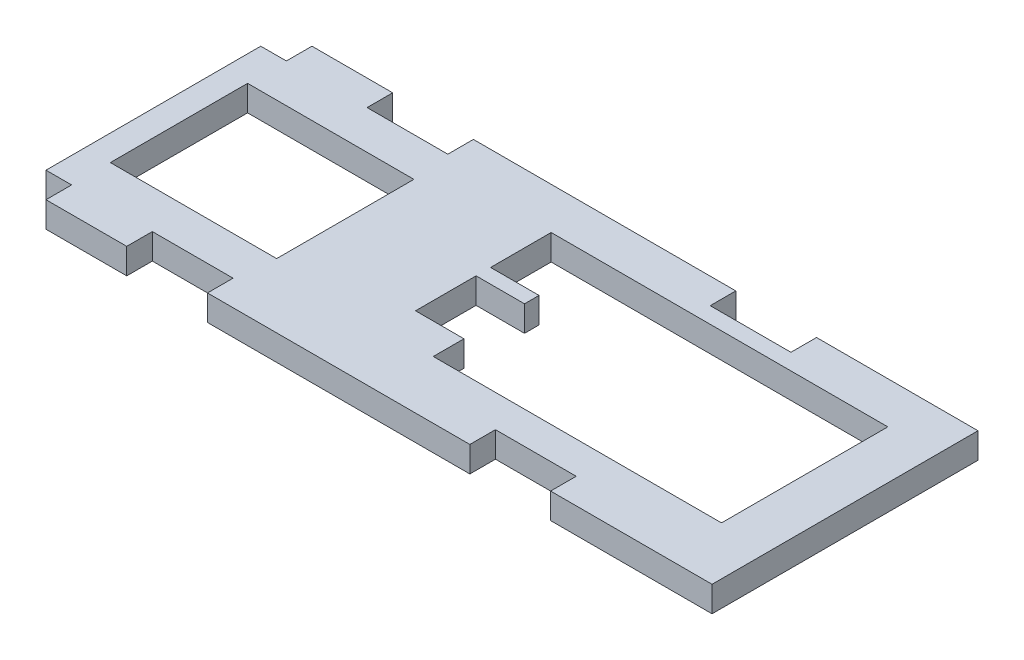
SolidWorks part; units mm, degrees
ref_plane "Front Plane" through (0, 0, 0) normal (0, 0, 1) x (1, 0, 0)
ref_plane "Top Plane" through (0, 0, 0) normal (0, 1, 0) x (1, 0, 0)
ref_plane "Right Plane" through (0, 0, 0) normal (1, 0, 0) x (0, 0, -1)
sketch "Sketch1" plane through (0, 0, 0) normal (0, 1, 0) x (1, 0, 0)
  line L0 (55.67, 32.94) -> (65.67, 32.94)
  line L1 (0, 0) -> (85.67, 0)
  line L2 (0, 0) -> (0, 32.94)
  line L3 (0, 32.94) -> (85.67, 32.94)
  line L4 (85.67, 0) -> (85.67, 32.94)
  line L5 (13.17, 3.17) -> (23.17, 3.17)
  line L6 (13.17, 3.17) -> (13.17, 0)
  line L7 (13.17, 0) -> (23.17, 0)
  line L8 (23.17, 3.17) -> (23.17, 0)
  line L9 (13.17, 32.94) -> (23.17, 32.94)
  line L10 (13.17, 32.94) -> (13.17, 29.77)
  line L11 (13.17, 29.77) -> (23.17, 29.77)
  line L12 (23.17, 32.94) -> (23.17, 29.77)
  line L13 (55.67, 32.94) -> (55.67, 29.77)
  line L14 (55.67, 29.77) -> (65.67, 29.77)
  line L15 (65.67, 32.94) -> (65.67, 29.77)
  line L16 (55.67, 3.17) -> (65.67, 3.17)
  line L17 (55.67, 3.17) -> (55.67, 0)
  line L18 (55.67, 0) -> (65.67, 0)
  line L19 (65.67, 3.17) -> (65.67, 0)
  line L25 (3.17, 24.97) -> (23.77, 24.97)
  line L26 (3.17, 24.97) -> (3.17, 7.97)
  line L27 (3.17, 7.97) -> (23.77, 7.97)
  line L28 (23.77, 24.97) -> (23.77, 7.97)
  line L29 (43.97, 27.77) -> (79.67, 27.77)
  line L30 (43.97, 27.77) -> (43.97, 7.17)
  line L31 (43.97, 7.17) -> (79.67, 7.17)
  line L32 (79.67, 27.77) -> (79.67, 7.17)
  line L33 (43.97, 10.97) -> (37.97, 10.97)
  line L34 (43.97, 10.97) -> (43.97, 18.47)
  line L35 (43.97, 18.47) -> (37.97, 18.47)
  line L36 (37.97, 10.97) -> (37.97, 18.47)
  line L37 (0, 32.94) -> (3.17, 32.94)
  line L38 (0, 32.94) -> (0, 29.77)
  line L39 (0, 29.77) -> (3.17, 29.77)
  line L40 (3.17, 32.94) -> (3.17, 29.77)
  line L41 (0, 0) -> (3.17, 0)
  line L42 (0, 0) -> (0, 3.17)
  line L43 (0, 3.17) -> (3.17, 3.17)
  line L44 (3.17, 0) -> (3.17, 3.17)
  line L45 (43.97, 20.27) -> (37.97, 20.27)
  line L46 (43.97, 20.27) -> (43.97, 27.77)
  line L47 (43.97, 27.77) -> (37.97, 27.77)
  line L48 (37.97, 20.27) -> (37.97, 27.77)
  point P35 (3.17, 16.47)
  point P39 (0, 16.47)
  dimension "D2" = 4
  dimension "D3" = 3.17
  dimension "D4" = 20.6
  dimension "D5" = 20.2
  dimension "D6" = 10
  dimension "D7" = 10
  dimension "D8" = 3.17
  dimension "D9" = 2
  dimension "D10" = 10
  dimension "D11" = 20
  dimension "D12" = 32.94
  dimension "D13" = 35.7
  dimension "D14" = 7.5
  dimension "D15" = 20.6
  dimension "D16" = 17
  dimension "D17" = 6
  dimension "D18" = 3.8
  dimension "D19" = 6
  dimension "D20" = 85.67
  dimension "D21" = 3.17
  dimension "D22" = 7.5
  dimension "D23" = 6
  dimension "D24" = 32.5
  dimension "D25" = 32.5
extrude "Boss-Extrude1" add sketch "Sketch1" against normal blind 3.17 contours L25 L28 L27 L2 L1 L6 L5 L8 L17 L16 L19 L4 L3 L15 L14 L13 L12 L11 L10 L29 L32 L31 L30
